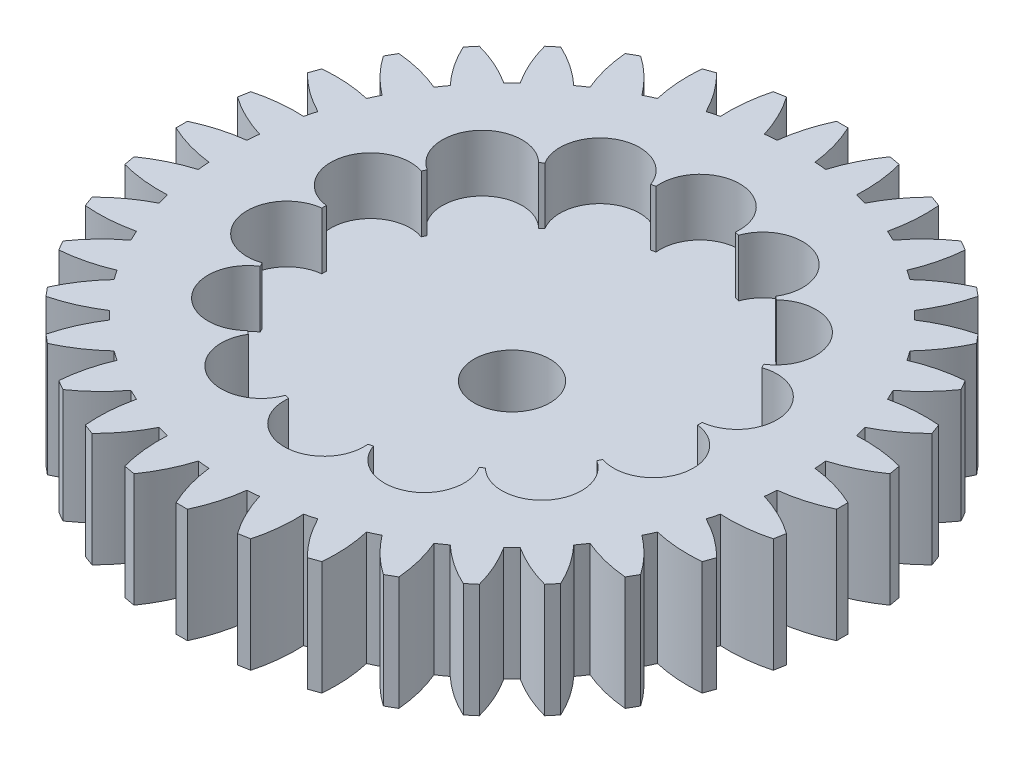
SolidWorks part; units mm, degrees
material "PBT General Purpose"
ref_plane "Front Plane" through (0, 0, 0) normal (0, 0, 1) x (1, 0, 0)
ref_plane "Top Plane" through (0, 0, 0) normal (0, 1, 0) x (1, 0, 0)
ref_plane "Right Plane" through (0, 0, 0) normal (1, 0, 0) x (0, 0, -1)
sketch "Sketch1" plane through (0, 0, 0) normal (0, 1, 0) x (1, 0, 0)
  circle A0 centre (0, 0) radius 7.5
  dimension "D1" = 15
extrude "Boss-Extrude1" add sketch "Sketch1" along normal blind 3
sketch "Sketch2" plane through (0, 3, 0) normal (0, 1, 0) x (1, 0, 0)
  line L0 (0, 0) -> (0, 8.7) construction
  line L1 (0, 0) -> (0.5, 7.4833) construction
  line L2 (0, 0) -> (-0.5, 7.4833) construction
  line L3 (-0.15, 8.7) -> (0.15, 8.7)
  circle A0 centre (0, 0) radius 7.5 construction
  arc A1 (-0.5, 7.4833) -> (-0.15, 8.7) centre (3.4707, 6.9998) cw
  arc A2 (0.15, 8.7) -> (0.5, 7.4833) centre (-3.4707, 6.9998) cw
  arc A3 (0.5, 7.4833) -> (-0.5, 7.4833) centre (0, 0) ccw
  point P10 (0, 8.7)
  dimension "D1" = 8.7
  dimension "D4" = 4
  dimension "D2" = 0.3
  dimension "D3" = 1
extrude "Boss-Extrude2" add sketch "Sketch2" against normal through all
pattern_circular "CirPattern1" count 36 over 360 about axis through (0, 0, 0) along (0, 1, 0) of "Boss-Extrude2"
sketch "Sketch5" plane through (0, 3, 0) normal (0, 1, 0) x (1, 0, 0)
  circle A0 centre (0, 0) radius 6
  circle A1 centre (0, 4.95) radius 1.05
  circle A2 centre (0, 0) radius 4.95
  dimension "D1" = 12
  dimension "D2" = 2.1
extrude "Cut-Extrude2" cut sketch "Sketch5" against normal blind 1.5 contours A1 A2 | A2 A1 | A1 A2
pattern_circular "CirPattern2" count 14 over 360 about axis through (0, 0, 0) along (0, 1, 0) of "Cut-Extrude2"
sketch "Sketch6" plane through (0, 1.5, 0) normal (0, 1, 0) x (1, 0, 0)
  circle A0 centre (0, 0) radius 1
  dimension "D1" = 2
extrude "Cut-Extrude3" cut sketch "Sketch6" against normal through all both and the other way through all
sketch "Sketch7" plane through (0, 0, 0) normal (0, -1, 0) x (1, 0, 0)
  line L0 (7.2973, 0.2) -> (6.9971, 0.2)
  line L1 (-0.2, 7.2973) -> (0.2, 7.2973)
  line L2 (-0.2, 7.2973) -> (-0.2, 6.9971)
  line L3 (-0.2, 6.9971) -> (0.2, 6.9971)
  line L4 (0.2, 7.2973) -> (0.2, 6.9971)
  line L5 (-0.2, 7.2973) -> (0.2, 6.9971) construction
  line L6 (-0.2, 6.9971) -> (0.2, 7.2973) construction
  line L7 (6.9971, 0.2) -> (6.9971, -0.2)
  line L8 (7.2973, 0.2) -> (7.2973, -0.2)
  line L9 (7.2973, -0.2) -> (6.9971, -0.2)
  line L10 (0.2, -7.2973) -> (0.2, -6.9971)
  line L11 (0.2, -6.9971) -> (-0.2, -6.9971)
  line L12 (0.2, -7.2973) -> (-0.2, -7.2973)
  line L13 (-0.2, -7.2973) -> (-0.2, -6.9971)
  line L14 (-7.2973, -0.2) -> (-6.9971, -0.2)
  line L15 (-6.9971, -0.2) -> (-6.9971, 0.2)
  line L16 (-7.2973, -0.2) -> (-7.2973, 0.2)
  line L17 (-7.2973, 0.2) -> (-6.9971, 0.2)
  circle A0 centre (0, 0) radius 7.3
  circle A1 centre (0, 0) radius 7
  arc A2 (-0.5, 7.4833) -> (-0.8071, 7.4565) centre (0, 0) ccw construction
  circle A3 centre (0, 0) radius 7
  circle A4 centre (0, 0) radius 7
  circle A5 centre (0, 0) radius 7
  point P7 (0, 7.1472)
  point P30 (0, 0)
  dimension "D1" = 0.2
  dimension "D2" = 0.3
  dimension "D3" = 0.4
  dimension "D4" = 4
extrude "Cut-Extrude4" cut sketch "Sketch7" against normal blind 0.2 contours A1 L2 A0 L17 | A1 L14 A0 L13 | A1 L10 A0 L9 | A1 L0 A0 L4
